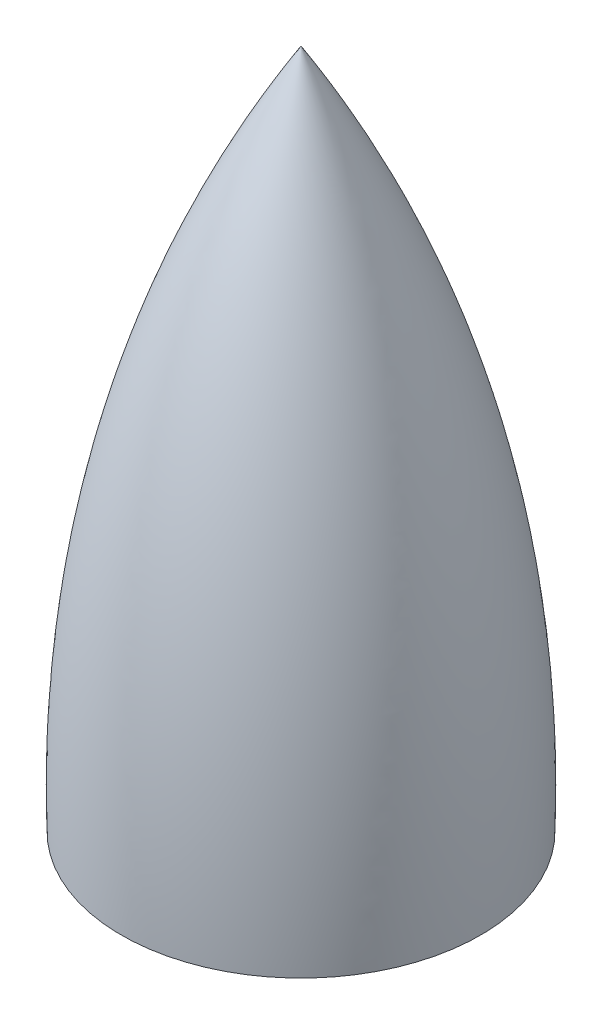
SolidWorks part; units mm, degrees
ref_plane "Front Plane" through (0, 0, 0) normal (0, 0, 1) x (1, 0, 0)
ref_plane "Top Plane" through (0, 0, 0) normal (0, 1, 0) x (1, 0, 0)
ref_plane "Right Plane" through (0, 0, 0) normal (1, 0, 0) x (0, 0, -1)
sketch "Sketch1" plane through (0, 0, 0) normal (0, 1, 0) x (1, 0, 0)
  circle A0 centre (0, 0) radius 101.6
sketch "Sketch2" plane through (0, 0, 0) normal (0, 0, 1) x (1, 0, 0)
  line L0 (0, 0) -> (0, 393.6864)
  line L1 (101.6, 0) -> (-101.6, 0) construction
  line L3 (0, 393.6864) -> (0, 377.4357)
  line L4 (-101.6, 0) -> (-104.775, 0)
  line L5 (-68.4237, 241.4942) -> (-71.5987, 241.4942)
  line L6 (0, 393.6864) -> (0, 396.8614)
  spline S0 degree 2 poles (-101.6, 0) (-107.046, 212.9876) (0, 393.6864) knots 0 0 0 1 1 1
  spline S1 degree 2 poles (-104.775, 0) (-110.9684, 215.5411) (0, 396.8614) knots 0 0 0 1 1 1
  dimension "D1" = 3.175
  dimension "D2" = 3.175
  dimension "D3" = 3.175
  dimension "D4" = 101.6
revolve "Revolve2" add sketch "Sketch2" angle 360 about L0
